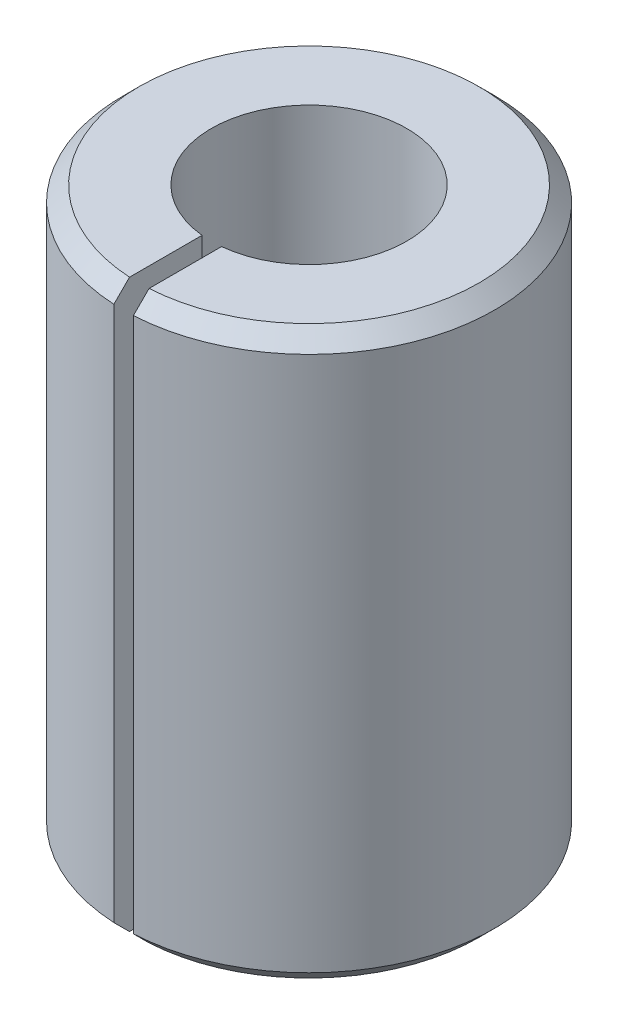
SolidWorks part; units mm, degrees
ref_plane "Front" through (0, 0, 0) normal (0, 0, 1) x (1, 0, 0)
ref_plane "Top" through (0, 0, 0) normal (0, 1, 0) x (1, 0, 0)
ref_plane "Right" through (0, 0, 0) normal (1, 0, 0) x (0, 0, -1)
sketch "Sketch1" plane through (0, 0, 0) normal (0, 1, 0) x (1, 0, 0)
  line L1 (-0.5, -5) -> (-0.5, -9.4868)
  line L2 (0.5, -5) -> (0.5, -9.4868)
  line L3 (-0.5, -5) -> (-0.5, -4.9749)
  line L4 (0.5, -5) -> (0.5, -4.9749)
  arc A0 (0.5, -9.4868) -> (-0.5, -9.4868) centre (0, 0) ccw
  arc A1 (0.5, -4.9749) -> (-0.5, -4.9749) centre (0, 0) ccw
  point P7 (0, -5)
  dimension "D1" = 19
  dimension "D2" = 10
  dimension "D3" = 1
extrude "Boss-Extrude1" add sketch "Sketch1" along normal blind 29
chamfer "Chamfer1" distance 0.8 angle 45 2 edges at (0, 0, -9.5) (0, 29, -9.5)
